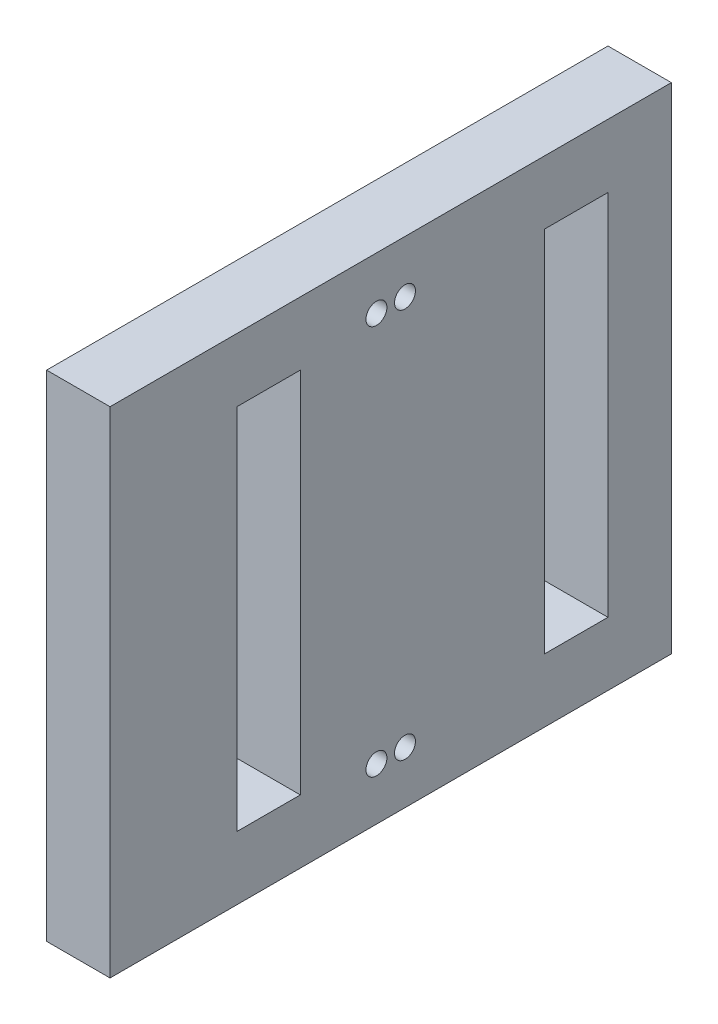
SolidWorks part; units mm, degrees
ref_plane "Front Plane" through (0, 0, 0) normal (0, 0, 1) x (1, 0, 0)
ref_plane "Top Plane" through (0, 0, 0) normal (0, 1, 0) x (1, 0, 0)
ref_plane "Right Plane" through (0, 0, 0) normal (1, 0, 0) x (0, 0, -1)
sketch "Sketch1" plane through (0, 0, 0) normal (1, 0, 0) x (0, 0, -1)
  line L1 (-44.25, 39) -> (44.25, 39)
  line L2 (-44.25, 39) -> (-44.25, -39)
  line L3 (-44.25, -39) -> (44.25, -39)
  line L4 (44.25, 39) -> (44.25, -39)
  line L5 (-44.25, 39) -> (44.25, -39) construction
  line L6 (-44.25, -39) -> (44.25, 39) construction
  line L7 (-24.25, 29) -> (-14.25, 29)
  line L8 (-24.25, 29) -> (-24.25, -29)
  line L9 (-24.25, -29) -> (-14.25, -29)
  line L10 (-14.25, 29) -> (-14.25, -29)
  line L11 (-24.25, 29) -> (-14.25, -29) construction
  line L12 (-24.25, -29) -> (-14.25, 29) construction
  line L13 (24.25, 29) -> (24.25, -29)
  line L14 (34.25, -29) -> (24.25, -29)
  line L15 (34.25, 29) -> (34.25, -29)
  line L16 (34.25, 29) -> (24.25, 29)
  point P0 (0, 0)
  point P6 (-19.25, 0)
  dimension "D1" = 88.5
  dimension "D2" = 78
  dimension "D3" = 10
  dimension "D4" = 20
  dimension "D5" = 58
  dimension "D6" = 10
  dimension "D7" = 10
  dimension "D8" = 58
extrude "Boss-Extrude1" add sketch "Sketch1" along normal blind 10
hole_wizard "M4 Tapped Hole1" positions "Sketch3" profile "Sketch4" tap size "M4" standard "ISO" end condition through all
sketch "Sketch3" plane through (10, 0, 0) normal (1, 0, 0) x (0, 0, -1)
  line L0 (0, 39) -> (0, -39) construction
  line L1 (44.25, 39) -> (-44.25, 39) construction
  line L2 (-44.25, -39) -> (44.25, -39) construction
  line L4 (-14.25, 0) -> (24.25, 0) construction
  line L5 (-14.25, -29) -> (-14.25, 29) construction
  line L6 (24.25, 29) -> (24.25, -29) construction
  point P0 (-2.25, -30.75)
  point P17 (-2.25, 30.75)
  point P19 (2.25, -30.75)
  point P20 (2.25, 30.75)
  dimension "D1" = 12
  dimension "D2" = 8.25
cosmetic thread "Hole Thread1" parameters "D2"=4
sketch "Sketch4" plane through (10, -30.75, 2.25) normal (0, 1, 0) x (0, 0, -1)
  line L0 (0, 0) -> (0, 10)
  line L1 (0, 10) -> (1.65, 10)
  line L2 (1.65, 10) -> (1.65, 0)
  line L5 (1.65, 0) -> (0, 0)
  line L11 (0, -6.35) -> (0, 107.95) construction
  dimension "Thru Tap Drill Dia." = 3.3
  dimension "Thru Tap Drill Depth" = 10
cosmetic thread "Hole Thread2" parameters "D2"=4
cosmetic thread "Hole Thread3" parameters "D2"=4
cosmetic thread "Hole Thread4" parameters "D2"=4
